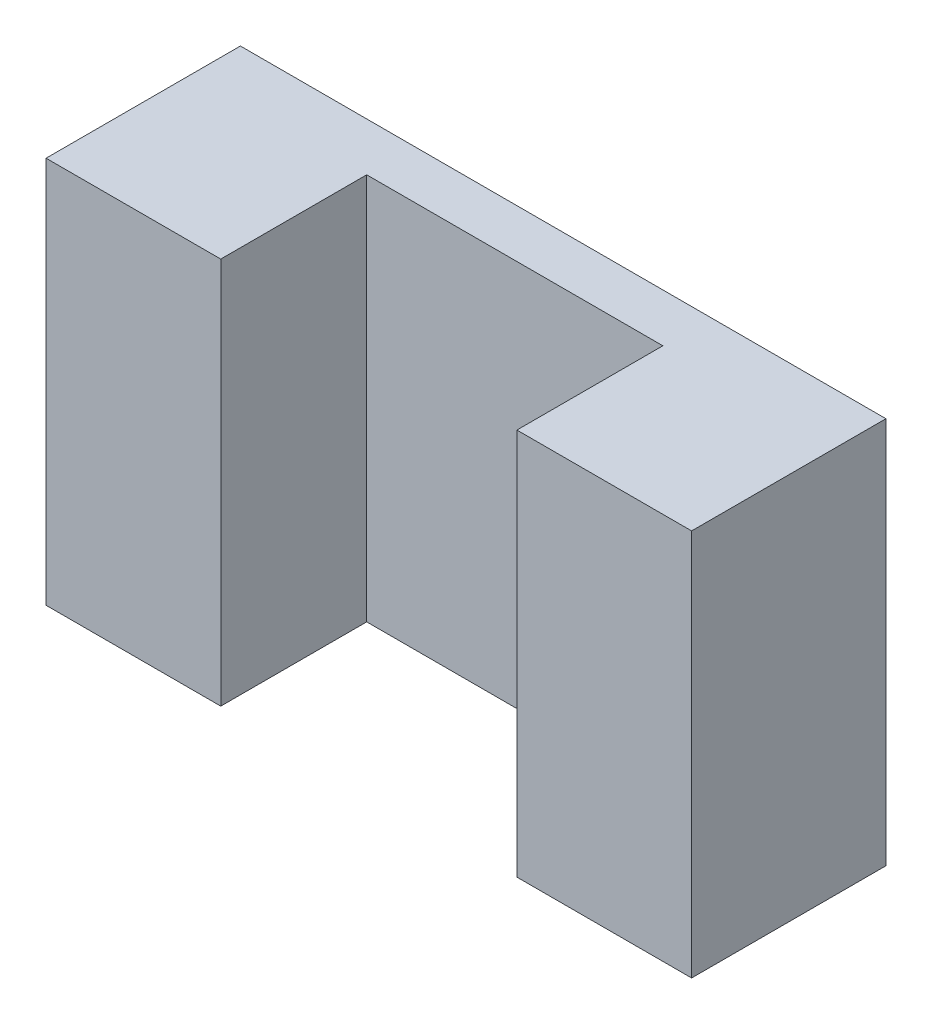
SolidWorks part; units mm, degrees
material "ABS"
ref_plane "Front Plane" through (0, 0, 0) normal (0, 0, 1) x (1, 0, 0)
ref_plane "Top Plane" through (0, 0, 0) normal (0, 1, 0) x (1, 0, 0)
ref_plane "Right Plane" through (0, 0, 0) normal (1, 0, 0) x (0, 0, -1)
sketch "Sketch1" plane through (0, 0, 0) normal (0, 0, 1) x (1, 0, 0)
  line L1 (33.2187, 19.925) -> (-33.2187, 19.925)
  line L2 (33.2187, 19.925) -> (33.2187, -19.925)
  line L3 (33.2187, -19.925) -> (-33.2187, -19.925)
  line L4 (-33.2187, 19.925) -> (-33.2187, -19.925)
  line L5 (33.2187, 19.925) -> (-33.2187, -19.925) construction
  line L6 (33.2187, -19.925) -> (-33.2187, 19.925) construction
  point P0 (0, 0)
  dimension "D1" = 39.85
  dimension "D2" = 66.4375
extrude "Boss-Extrude1" add sketch "Sketch1" along normal blind 20
sketch "Sketch2" plane through (0, 0, 20) normal (0, 0, 1) x (1, 0, 0)
  line L0 (-33.2187, -19.925) -> (33.2187, -19.925) construction
  line L1 (15.24, 19.925) -> (-15.24, 19.925)
  line L2 (15.24, 19.925) -> (15.24, -19.925)
  line L3 (15.24, -19.925) -> (-15.24, -19.925)
  line L4 (-15.24, 19.925) -> (-15.24, -19.925)
  line L5 (15.24, 19.925) -> (-15.24, -19.925) construction
  line L6 (15.24, -19.925) -> (-15.24, 19.925) construction
  point P0 (0, 0)
  dimension "D1" = 30.48
extrude "Cut-Extrude1" cut sketch "Sketch2" against normal blind 15.02
